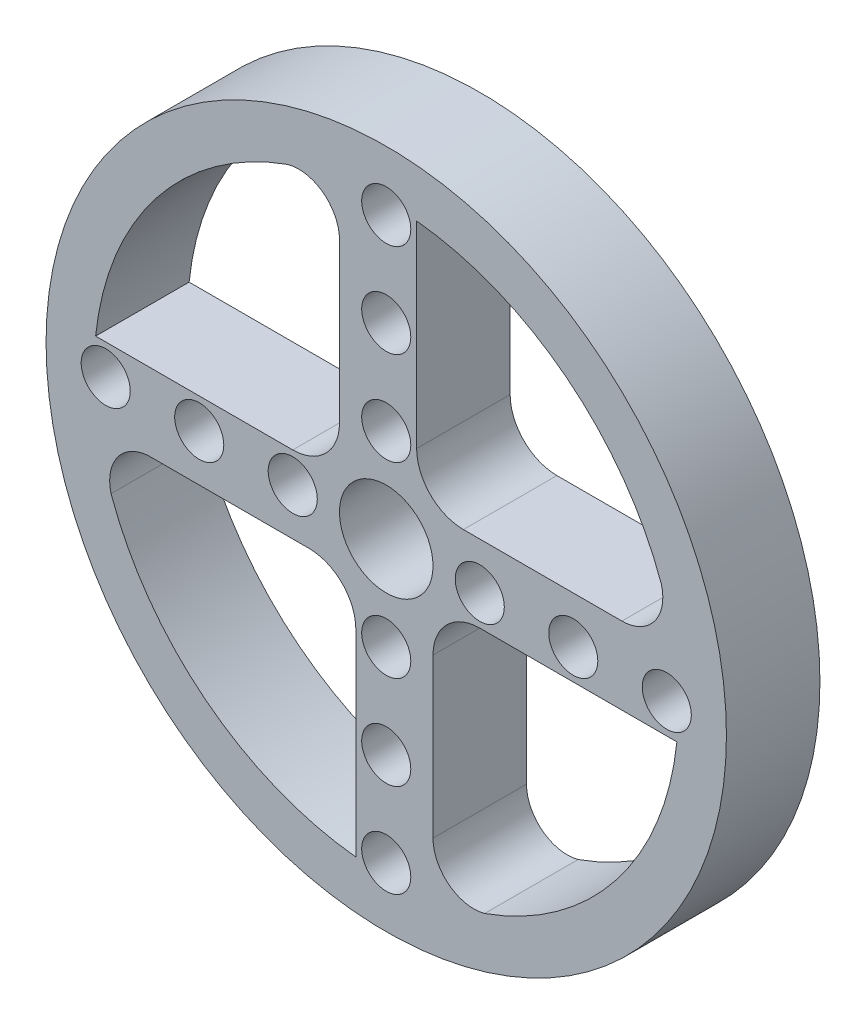
SolidWorks part; units mm, degrees
material "6061-T4 (SS)"
ref_plane "Alzado" through (0, 0, 0) normal (0, 0, 1) x (1, 0, 0)
ref_plane "Planta" through (0, 0, 0) normal (0, 1, 0) x (1, 0, 0)
ref_plane "Vista lateral" through (0, 0, 0) normal (1, 0, 0) x (0, 0, -1)
sketch "Croquis1" plane through (0, 0, 0) normal (0, 0, 1) x (1, 0, 0)
  line L1 (0, -55) -> (0, 55) construction
  line L2 (0, -4) -> (-20.1629, -4)
  line L3 (-4, 0) -> (-4, 20.1629)
  line L4 (0, 4) -> (20.1629, 4)
  line L5 (4, 0) -> (4, -20.1629)
  line L6 (-24.8644, 2.6) -> (-8, 2.6)
  line L7 (55, 0) -> (-55, 0) construction
  line L8 (2.6, 24.8644) -> (2.6, 8)
  line L9 (24.8644, -2.6) -> (8, -2.6)
  line L10 (-2.6, -24.8644) -> (-2.6, -8)
  circle A0 centre (0, 0) radius 29.105
  circle A1 centre (0, 0) radius 24 construction
  circle A2 centre (0, 0) radius 16 construction
  circle A3 centre (0, 0) radius 8 construction
  circle A4 centre (0, 0) radius 4
  circle A5 centre (-24, 0) radius 2.1
  circle A6 centre (-16, 0) radius 2.1
  circle A7 centre (-8, 0) radius 2.1
  circle A8 centre (0, 24) radius 2.1
  circle A9 centre (0, 16) radius 2.1
  circle A10 centre (0, 8) radius 2.1
  circle A11 centre (24, 0) radius 2.1
  circle A12 centre (16, 0) radius 2.1
  circle A13 centre (8, 0) radius 2.1
  circle A14 centre (0, -24) radius 2.1
  circle A15 centre (0, -16) radius 2.1
  circle A16 centre (0, -8) radius 2.1
  circle A17 centre (0, 0) radius 25
  arc A18 (-20.1629, -4) -> (-23.5411, -8.4153) centre (-20.1629, -7.5) ccw
  arc A19 (-4, 20.1629) -> (-8.4153, 23.5411) centre (-7.5, 20.1629) ccw
  arc A20 (20.1629, 4) -> (23.5411, 8.4153) centre (20.1629, 7.5) ccw
  arc A21 (4, -20.1629) -> (8.4153, -23.5411) centre (7.5, -20.1629) ccw
  arc A22 (-8, 2.6) -> (-4, 6.6) centre (-8, 6.6) ccw
  arc A23 (2.6, 8) -> (6.6, 4) centre (6.6, 8) ccw
  arc A24 (8, -2.6) -> (4, -6.6) centre (8, -6.6) ccw
  arc A25 (-2.6, -8) -> (-6.6, -4) centre (-6.6, -8) ccw
  point P34 (0, 0)
  point P54 (0, 0)
  point P73 (0, 0)
  dimension "D1" = 58.21
  dimension "D2" = 48
  dimension "D3" = 32
  dimension "D4" = 16
  dimension "D5" = 8
  dimension "D6" = 4.2
  dimension "D8" = 50
  dimension "D9" = 3.5
  dimension "D11" = 2.6
  dimension "D7" = 4
  dimension "D10" = 4
  dimension "D12" = 4
extrude "Saliente-Extruir1" add sketch "Croquis1" along normal blind 8 contours A0 A17 A11 A14 A5 A8 | A22 L6 A17 A5 A18 L2 A4 L3 A7 A6 | A25 L10 A17 A14 A21 L5 A4 L2 A15 A16 | A24 L9 A17 A11 A20 L4 A4 L5 A13 A12 | A23 L8 A17 A8 A19 L3 A4 L4 A10 A9
